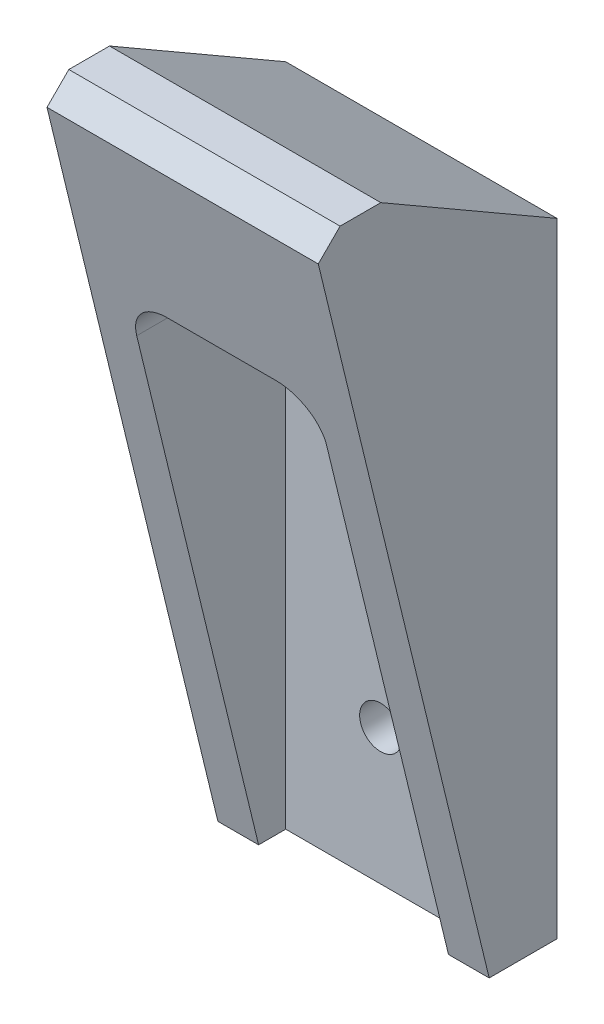
SolidWorks part; units mm, degrees
ref_plane "Front Plane" through (0, 0, 0) normal (0, 0, 1) x (1, 0, 0)
ref_plane "Top Plane" through (0, 0, 0) normal (0, 1, 0) x (1, 0, 0)
ref_plane "Right Plane" through (0, 0, 0) normal (1, 0, 0) x (0, 0, -1)
sketch "Sketch1" plane through (0, 0, 0) normal (1, 0, 0) x (0, 0, -1)
  line L0 (0, 0) -> (-5, 0)
  line L1 (0, 0) -> (0, 46)
  line L2 (0, 46) -> (-12.9904, 53.5)
  line L3 (-12.9904, 53.5) -> (-17.9904, 53.5)
  line L4 (-17.9904, 53.5) -> (-5, 0)
  dimension "D1" = 5
  dimension "D2" = 46
  dimension "D3" = 120
  dimension "D4" = 15
  dimension "D5" = 5
extrude "Boss-Extrude1" add sketch "Sketch1" along normal blind 20
ref_plane "Plane1" through (0, 0, 0) normal (0, -1, 0) x (-1, 0, 0)
ref_point "Point1"
ref_plane "Plane2" through (0, 0, 17.9904) normal (0, 0, 1) x (1, 0, 0)
sketch "Sketch4" plane through (0, 0, 17.9904) normal (0, 0, 1) x (1, 0, 0)
  line L0 (10, 0) -> (10, 53.5) construction
  line L1 (0, 0) -> (3, 0)
  line L2 (20, 0) -> (17, 0)
  line L3 (3, 0) -> (3, 40)
  line L4 (0, 53.5) -> (0, 0)
  line L5 (0, 0) -> (20, 0)
  line L6 (20, 0) -> (20, 53.5)
  line L7 (20, 53.5) -> (0, 53.5)
  line L8 (0, 53.5) -> (0, 0)
  line L9 (0, 0) -> (20, 0)
  line L10 (20, 0) -> (20, 53.5)
  line L11 (20, 53.5) -> (0, 53.5)
  line L12 (3, 40) -> (17, 40)
  line L13 (17, 40) -> (17, 0)
  dimension "D2" = 3
  dimension "D3" = 3
  dimension "D4" = 40
  dimension "D1" = 0
extrude "Cut-Extrude1" cut sketch "Sketch4" against normal offset from surface (14.9904 mm away) 3 contours L0 L9 L13 L12 | L9 L0 L12 L3
sketch "Sketch5" plane through (0, 0, 3) normal (0, 0, 1) x (1, 0, 0)
  line L0 (10, 0) -> (10, 53.1114) construction
  line L1 (17, 0) -> (3, 0) construction
  line L2 (17, 40) -> (3, 40) construction
  point P4 (10, 10)
  point P5 (10, 30)
  dimension "D1" = 10
  dimension "D2" = 10
fillet "Fillet1" radius 3 2 edges at (3, 40, 8.8562) (17, 40, 8.8562)
chamfer "Chamfer1" distance 2 angle 45 1 edges at (10, 53.5, 17.9904)
hole_wizard "M3 Clearance" positions "3DSketch1" profile "Sketch7" hole size "M" standard "ANSI Inch" end condition through all
sketch3d "3DSketch1"
  point P0 (10, 30, 3)
  point P3 (10, 10, 3)
sketch "Sketch7" plane through (10, 30, 3) normal (1, 0, 0) x (0, -1, 0)
  line L0 (0, 0) -> (0, 3)
  line L1 (0, 3) -> (1.55, 3)
  line L2 (1.55, 3) -> (1.55, 0)
  line L5 (1.55, 0) -> (0, 0)
  line L11 (0, -6.35) -> (0, 107.95) construction
  dimension "Thru Hole Dia." = 3.1
  dimension "Thru Hole Depth" = 3
